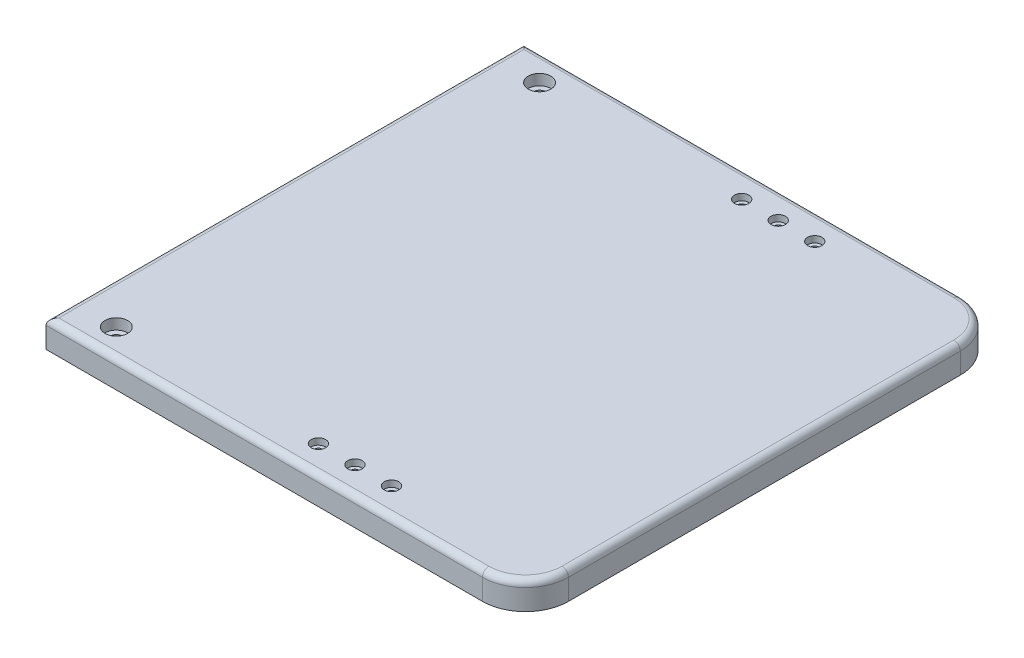
SolidWorks part; units mm, degrees
ref_plane "Front Plane" through (0, 0, 0) normal (0, 0, 1) x (1, 0, 0)
ref_plane "Top Plane" through (0, 0, 0) normal (0, 1, 0) x (1, 0, 0)
ref_plane "Right Plane" through (0, 0, 0) normal (1, 0, 0) x (0, 0, -1)
sketch "Sketch2" plane through (0, 0, 0) normal (0, 1, 0) x (1, 0, 0)
  line L1 (-111.5, 111.125) -> (111.5, 111.125)
  line L2 (-111.5, 111.125) -> (-111.5, -111.125)
  line L3 (-111.5, -111.125) -> (111.5, -111.125)
  line L4 (111.5, 111.125) -> (111.5, -111.125)
  line L5 (-111.5, 111.125) -> (111.5, -111.125) construction
  line L6 (-111.5, -111.125) -> (111.5, 111.125) construction
  point P0 (0, 0)
  dimension "D2" = 222.25
  dimension "D1" = 223
extrude "Boss-Extrude1" add sketch "Sketch2" along normal blind 12.7
fillet "Fillet6" radius 20 2 edges at (111.5, 6.35, -111.125) (111.5, 6.35, 111.125)
fillet "Fillet5" radius 3 6 edges at (-10, 12.7, 111.125) (-111.5, 12.7, 0) (-10, 12.7, -111.125) (111.5, 12.7, 0) (105.6421, 12.7, 105.2671) (105.6421, 12.7, -105.2671)
sketch "Sketch4" plane through (0, 12.7, 0) normal (0, 1, 0) x (1, 0, 0)
  line L0 (0, 0) -> (-45.9035, 0) construction
  line L1 (0, 0) -> (0, -26.5712) construction
  line L2 (91.5, -111.125) -> (-111.5, -111.125) construction
  line L3 (-111.5, -111.125) -> (-111.5, 111.125) construction
  line L4 (111.5, 91.125) -> (111.5, -91.125) construction
  point P0 (-91.5, -98.425)
  point P9 (19.5, 98.425)
  point P10 (36.5, -98.425)
  point P11 (2.5, -98.425)
  point P12 (0, 0)
  point P13 (36.5, 98.425)
  point P14 (-91.5, 98.425)
  point P15 (2.5, 98.425)
  point P16 (0, 0)
  point P21 (19.5, -98.425)
  dimension "D1" = 12.7
  dimension "D2" = 20
  dimension "D3" = 75
  dimension "D4" = 17
  dimension "D5" = 17
hole_wizard "CBORE for M3 SBHCS1" positions "Sketch5" profile "Sketch6" counterbore size "M3" standard "ANSI Metric" end condition up to next
sketch "Sketch5" plane through (0, 12.7, 0) normal (0, 1, 0) x (1, 0, 0)
  point P3 (36.5, -98.425)
  point P6 (36.5, 98.425)
  point P12 (19.5, -98.425)
  point P15 (19.5, 98.425)
  point P18 (2.5, -98.425)
  point P22 (2.5, 98.425)
sketch "Sketch6" plane through (36.5, 12.7, 98.425) normal (1, 0, 0) x (0, 0, 1)
  line L0 (0, 0) -> (0, 12.7)
  line L1 (0, 12.7) -> (1.7, 12.7)
  line L3 (1.7, 12.7) -> (1.7, 3)
  line L4 (1.7, 3) -> (3.35, 3)
  line L5 (3.35, 3) -> (3.35, 0)
  line L7 (3.35, 0) -> (0, 0)
  line L11 (0, -6.35) -> (0, 107.95) construction
  dimension "Thru Hole Dia." = 3.4
  dimension "Thru Hole Depth" = 12.7
  dimension "C'Bore Dia." = 6.7
  dimension "C'Bore Depth" = 3
hole_wizard "CBORE for M5 SBHCS1" positions "Sketch7" profile "Sketch8" counterbore size "M5" standard "ANSI Metric" end condition up to next
sketch "Sketch7" plane through (0, 12.7, 0) normal (0, 1, 0) x (1, 0, 0)
  point P0 (-91.5, 98.425)
  point P3 (-91.5, -98.425)
sketch "Sketch8" plane through (-91.5, 12.7, -98.425) normal (1, 0, 0) x (0, 0, 1)
  line L0 (0, 0) -> (0, 12.7)
  line L1 (0, 12.7) -> (2.75, 12.7)
  line L3 (2.75, 12.7) -> (2.75, 5)
  line L4 (2.75, 5) -> (5.25, 5)
  line L5 (5.25, 5) -> (5.25, 0)
  line L7 (5.25, 0) -> (0, 0)
  line L11 (0, -6.35) -> (0, 107.95) construction
  dimension "Thru Hole Dia." = 5.5
  dimension "Thru Hole Depth" = 12.7
  dimension "C'Bore Dia." = 10.5
  dimension "C'Bore Depth" = 5
sketch "Sketch9" plane through (0, 0, 0) normal (0, -1, 0) x (1, 0, 0)
  line L0 (0, 0) -> (-45.9035, 0) construction
  circle A0 centre (-91.5, 98.425) radius 6.5
  circle A1 centre (-91.5, -98.425) radius 6.5
  point P9 (0, 0)
  point P10 (-76.9262, 101.7855)
  dimension "D1" = 13
extrude "Cut-Extrude1" cut sketch "Sketch9" against normal blind 2
equation "\"Length\"=250"
equation "\"Width\"=222.25"
equation "\"D2@Sketch2\"=\"Width\""
